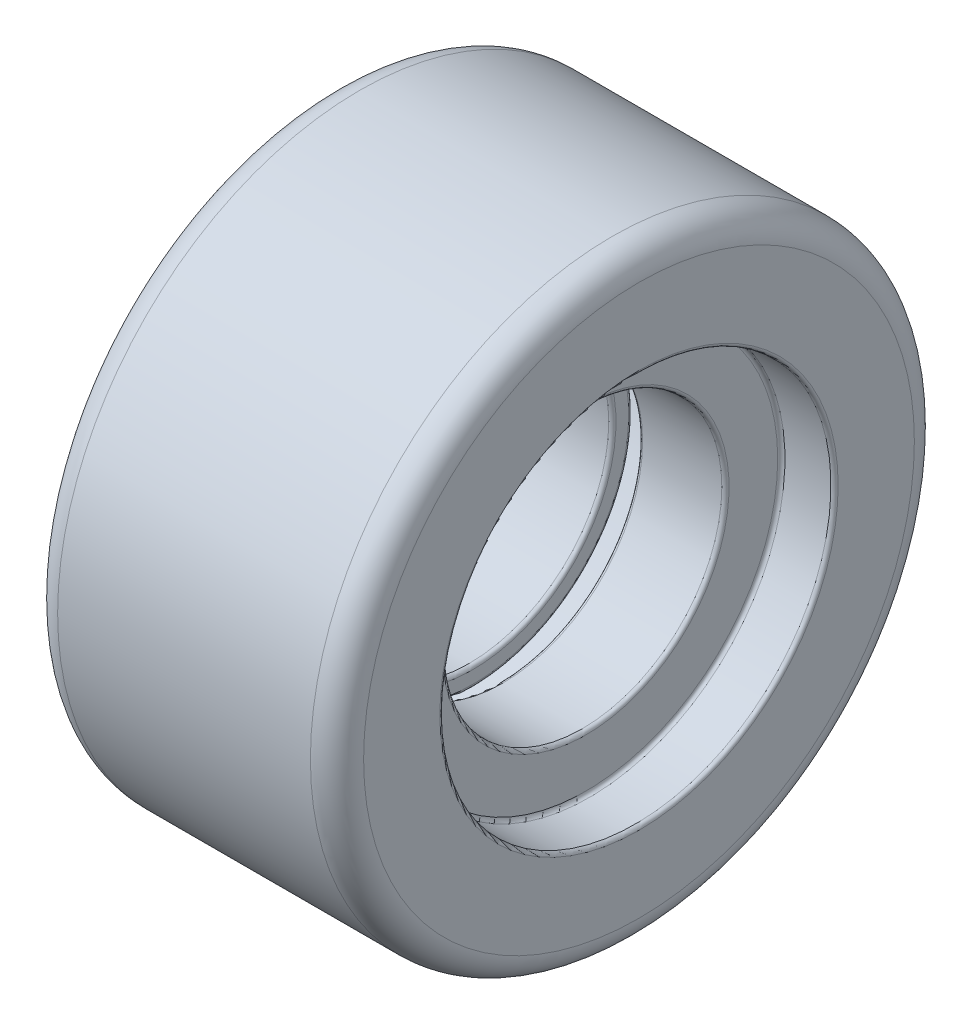
SolidWorks part; units mm, degrees
ref_plane "Front Plane" through (0, 0, 0) normal (0, 0, 1) x (1, 0, 0)
ref_plane "Top Plane" through (0, 0, 0) normal (0, 1, 0) x (1, 0, 0)
ref_plane "Right Plane" through (0, 0, 0) normal (1, 0, 0) x (0, 0, -1)
sketch "Sketch1" plane through (0, 0, 0) normal (0, 0, 1) x (1, 0, 0)
  line L0 (0, 65.3425) -> (0, -68.9041) construction
  line L1 (-91.3699, 0) -> (107.8082, 0) construction
  line L2 (57.2852, 120) -> (12.7148, 120)
  line L3 (60, 122.7148) -> (60, 159.2852)
  line L4 (62.7148, 162) -> (97.2852, 162)
  line L5 (100, 164.7148) -> (100, 209.2852)
  line L6 (97.2852, 212) -> (-97.2852, 212)
  line L7 (10, 117.2852) -> (10, 107.7148)
  line L8 (12.7148, 105) -> (72.2852, 105)
  line L9 (75, 107.7148) -> (75, 144.2852)
  line L10 (77.7148, 147) -> (112.2852, 147)
  line L11 (115, 149.7148) -> (115, 207)
  line L12 (95, 227) -> (-95, 227)
  line L13 (-115, 149.7148) -> (-115, 207)
  line L14 (-75, 147) -> (-112.2852, 147)
  line L15 (-75, 107.7148) -> (-75, 147)
  line L16 (-12.7148, 105) -> (-72.2852, 105)
  line L17 (-10, 117.2852) -> (-10, 107.7148)
  line L18 (-100, 164.7148) -> (-100, 209.2852)
  line L19 (-62.7148, 162) -> (-97.2852, 162)
  line L20 (-60, 122.7148) -> (-60, 159.2852)
  line L21 (-57.2852, 120) -> (-12.7148, 120)
  arc A0 (100, 209.2852) -> (97.2852, 212) centre (97.2852, 209.2852) ccw
  arc A1 (112.2852, 147) -> (115, 149.7148) centre (112.2852, 149.7148) ccw
  arc A2 (97.2852, 162) -> (100, 164.7148) centre (97.2852, 164.7148) ccw
  arc A3 (75, 144.2852) -> (77.7148, 147) centre (77.7148, 144.2852) cw
  arc A4 (60, 159.2852) -> (62.7148, 162) centre (62.7148, 159.2852) cw
  arc A5 (72.2852, 105) -> (75, 107.7148) centre (72.2852, 107.7148) ccw
  arc A6 (57.2852, 120) -> (60, 122.7148) centre (57.2852, 122.7148) ccw
  arc A7 (10, 107.7148) -> (12.7148, 105) centre (12.7148, 107.7148) ccw
  arc A8 (12.7148, 120) -> (10, 117.2852) centre (12.7148, 117.2852) ccw
  arc A9 (-12.7148, 105) -> (-10, 107.7148) centre (-12.7148, 107.7148) ccw
  arc A10 (-10, 117.2852) -> (-12.7148, 120) centre (-12.7148, 117.2852) ccw
  arc A11 (-60, 122.7148) -> (-57.2852, 120) centre (-57.2852, 122.7148) ccw
  arc A12 (-75, 107.7148) -> (-72.2852, 105) centre (-72.2852, 107.7148) ccw
  arc A13 (-115, 149.7148) -> (-112.2852, 147) centre (-112.2852, 149.7148) ccw
  arc A14 (-62.7148, 162) -> (-60, 159.2852) centre (-62.7148, 159.2852) cw
  arc A15 (-100, 209.2852) -> (-97.2852, 212) centre (-97.2852, 209.2852) cw
  arc A16 (-100, 164.7148) -> (-97.2852, 162) centre (-97.2852, 164.7148) ccw
  arc A17 (115, 207) -> (95, 227) centre (95, 207) ccw
  arc A18 (-115, 207) -> (-95, 227) centre (-95, 207) cw
  point P18 (0, 227)
  point P24 (0, 212)
  point P29 (100, 212)
  point P32 (115, 147)
  point P35 (100, 162)
  point P38 (75, 147)
  point P41 (60, 162)
  point P44 (75, 105)
  point P47 (60, 120)
  point P50 (10, 105)
  point P53 (10, 120)
  point P56 (-10, 105)
  point P59 (-10, 120)
  point P62 (-60, 120)
  point P65 (-75, 105)
  point P68 (-115, 147)
  point P71 (-60, 162)
  point P74 (-100, 212)
  point P77 (-100, 162)
  point P80 (115, 227)
  point P83 (-115, 227)
  dimension "D12" = 2.7148
  dimension "D13" = 20
  dimension "D1" = 10
  dimension "D2" = 15
  dimension "D3" = 15
  dimension "D4" = 15
  dimension "D5" = 15
  dimension "D6" = 50
  dimension "D7" = 40
  dimension "D8" = 120
  dimension "D9" = 15
  dimension "D10" = 42
  dimension "D11" = 80
revolve "Revolve1" add sketch "Sketch1" angle 360 about L1
